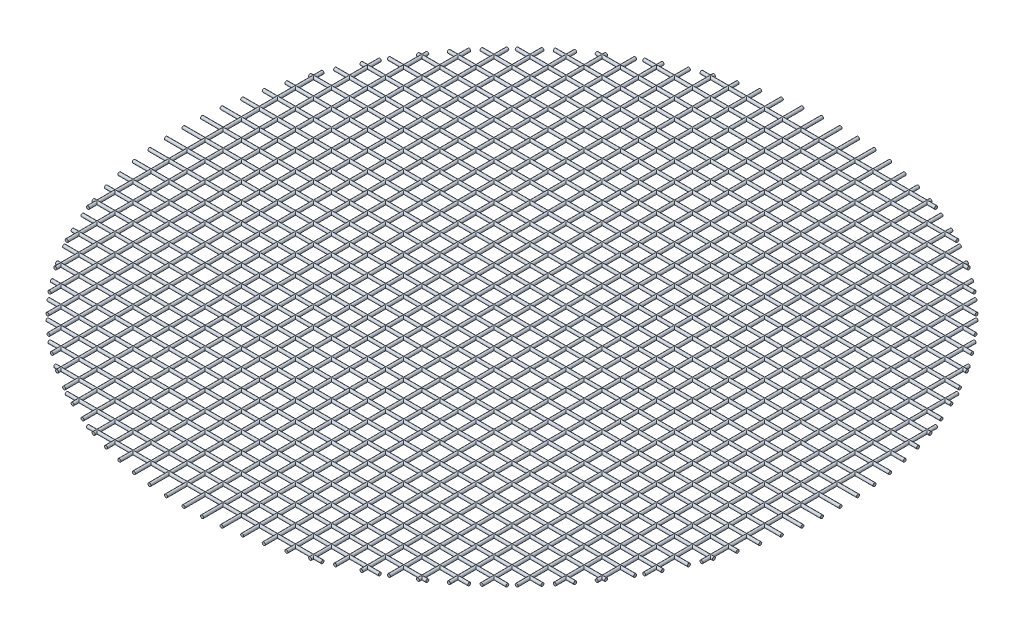
SolidWorks part; units mm, degrees
ref_plane "Front Plane" through (0, 0, 0) normal (0, 0, 1) x (1, 0, 0)
ref_plane "Top Plane" through (0, 0, 0) normal (0, 1, 0) x (1, 0, 0)
ref_plane "Right Plane" through (0, 0, 0) normal (1, 0, 0) x (0, 0, -1)
sketch "Sketch1" plane through (0, 0, 0) normal (0, 1, 0) x (1, 0, 0)
  line L0 (0, 2413) -> (0, -2413)
  line L1 (-2540, 0) -> (2540, 0)
  point P4 (0, 0)
  point P8 (0, 0)
  dimension "D1" = 4826
  dimension "D2" = 5080
sketch "Sketch13" plane through (0, 0, 0) normal (0, 1, 0) x (1, 0, 0)
  circle A0 centre (0, 0) radius 2311.4
  dimension "D1" = 4622.8
sketch "Sketch14" plane through (0, 0, 0) normal (0, 1, 0) x (1, 0, 0)
  line L0 (-2540, 0) -> (2540, 0) construction
  line L1 (-2311.4, 0) -> (2311.4, 0)
  line L2 (-2307.9084, 127) -> (2307.9084, 127)
  line L3 (-2297.4016, 254) -> (2297.4016, 254)
  line L4 (-2279.7827, 381) -> (2279.7827, 381)
  line L5 (-2254.8849, 508) -> (2254.8849, 508)
  line L6 (-2222.4637, 635) -> (2222.4637, 635)
  line L7 (-2182.1838, 762) -> (2182.1838, 762)
  line L8 (-2133.6, 889) -> (2133.6, 889)
  line L9 (-2076.1296, 1016) -> (2076.1296, 1016)
  line L10 (-2009.0099, 1143) -> (2009.0099, 1143)
  line L11 (-1931.2353, 1270) -> (1931.2353, 1270)
  line L12 (-1841.4562, 1397) -> (1841.4562, 1397)
  line L13 (-1737.813, 1524) -> (1737.813, 1524)
  line L14 (-1617.643, 1651) -> (1617.643, 1651)
  line L15 (-1476.9177, 1778) -> (1476.9177, 1778)
  line L16 (-1309.0244, 1905) -> (1309.0244, 1905)
  line L17 (-1101.6106, 2032) -> (1101.6106, 2032)
  line L18 (-825.4023, 2159) -> (825.4023, 2159)
  circle A0 centre (0, 0) radius 2311.4 construction
  circle A1 centre (0, 0) radius 2311.4 construction
  dimension "D2" = 127
  dimension "D1" = 18
sketch "Sketch15" plane through (0, 0, 0) normal (0, 1, 0) x (1, 0, 0)
  line L0 (0, 2413) -> (0, -2413) construction
  line L1 (0, 2311.4) -> (0, -2311.4)
  line L2 (127, 2307.9084) -> (127, -2307.9084)
  line L3 (254, 2297.4016) -> (254, -2297.4016)
  line L4 (381, 2279.7827) -> (381, -2279.7827)
  line L5 (508, 2254.8849) -> (508, -2254.8849)
  line L6 (635, 2222.4637) -> (635, -2222.4637)
  line L7 (762, 2182.1838) -> (762, -2182.1838)
  line L8 (889, 2133.6) -> (889, -2133.6)
  line L9 (1016, 2076.1296) -> (1016, -2076.1296)
  line L10 (1143, 2009.0099) -> (1143, -2009.0099)
  line L11 (1270, 1931.2353) -> (1270, -1931.2353)
  line L12 (1397, 1841.4562) -> (1397, -1841.4562)
  line L13 (1524, 1737.813) -> (1524, -1737.813)
  line L14 (1651, 1617.643) -> (1651, -1617.643)
  line L15 (1778, 1476.9177) -> (1778, -1476.9177)
  line L16 (1905, 1309.0244) -> (1905, -1309.0244)
  line L17 (2032, 1101.6106) -> (2032, -1101.6106)
  line L18 (2159, 825.4023) -> (2159, -825.4023)
  circle A1 centre (0, 0) radius 2311.4
  circle A2 centre (0, 0) radius 2311.4 construction
  dimension "D3" = 127
  dimension "D1" = 0
  dimension "D2" = 18
other "Pipe 0.5 SCH 40(17)"
ref_plane "Plane1" through (-825.4023, 0, -2159) normal (1, 0, 0) x (0, 0, -1)
sketch "Sketch11" plane through (-825.4023, 0, -2159) normal (1, 0, 0) x (0, 0, -1)
  circle A1 centre (0, 0) radius 10.668
  circle A2 centre (0, 0) radius 6.35 construction
  point P5 (0, 0)
  dimension "Out_dia" = 21.336
  dimension "D1" = 12.7
other "Pipe 0.5 SCH 40(16)"
ref_plane "Plane2" through (2159, 0, -825.4023) normal (0, 0, 1) x (1, 0, 0)
sketch "Sketch12" plane through (2159, 0, -825.4023) normal (0, 0, 1) x (1, 0, 0)
  circle A1 centre (0, 0) radius 10.668
  circle A2 centre (0, 0) radius 6.35 construction
  point P5 (0, 0)
  dimension "Out_dia" = 21.336
  dimension "D1" = 12.7
mirror "Mirror1" about plane through (0, 0, 0) normal (0, 0, 1) of bodies 536 535 534 533 532 544 531 543 530 542 529 541 528 540 539 538 537
mirror "Mirror2" about plane through (0, 0, 0) normal (1, 0, 0) of bodies 557 556 555 554 553 552 551 550 562 549 561 548 560 547 559 546 558
